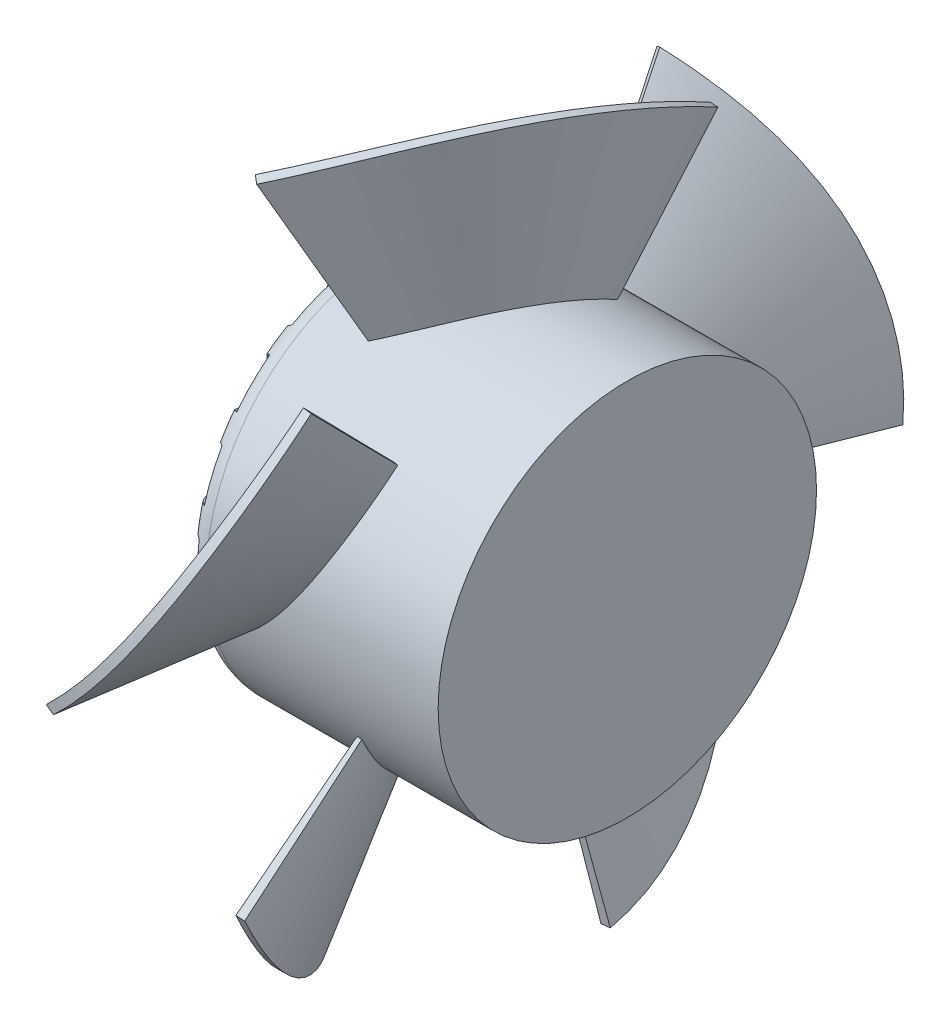
SolidWorks part; units mm, degrees
material "PW100:Mi:0:30:C1:0:1:2:Re:16:"
ref_plane "Front" through (0, 0, 0) normal (0, 0, 1) x (1, 0, 0)
ref_plane "Top" through (0, 0, 0) normal (0, 1, 0) x (1, 0, 0)
ref_plane "Right" through (0, 0, 0) normal (1, 0, 0) x (0, 0, -1)
sketch "Support-Front" plane through (0, 0, 0) normal (0, 0, 1) x (1, 0, 0)
  line L0 (-32, 0) -> (-5, 0) construction
  line L1 (-32, -20) -> (-32, 20)
  line L2 (-32, 20) -> (-5, 20)
  line L3 (-32, -20) -> (-5, -20)
  line L4 (-5, 20) -> (-5, -20)
  line L5 (-18.5, 20) -> (-18.5, -20) construction
  line L6 (-5, 20) -> (0, 20) construction
  line L7 (-5, -20) -> (0, -20) construction
  line L8 (0, 20) -> (0, -20) construction
  line L11 (-18.5, 20) -> (-18.5, 37) construction
  line L12 (-18.5, -20) -> (-18.5, -37) construction
  point P12 (0, 0)
  point P14 (-18.5, 0)
  dimension "Width" = 32
  dimension "Diam-Body" = 40
  dimension "Diam-Fan" = 74
  dimension "Dist-Fan" = 5
sketch "Support-Right" plane through (0, 0, 0) normal (1, 0, 0) x (0, 0, -1)
  line L0 (0, 0) -> (-3.3333, 0) construction
  line L1 (-3.3333, 0) -> (-6.6667, 0) construction
  line L2 (0, 20) -> (-2.4557, 19.1062) construction
  line L3 (-6.6667, 0) -> (-10, 0) construction
  line L4 (-10, 0) -> (-13.3333, 0) construction
  line L6 (0, 20) -> (0, -20) construction
  line L7 (0, 20) -> (0, -20) construction
  line L8 (2.4557, 20) -> (2.4557, 19.1062)
  line L9 (-2.4557, 20) -> (-2.4557, 19.1062)
  line L10 (2.4557, 20) -> (-2.4557, 20)
  line L11 (0, 20) -> (0, 19.1062) construction
  line L12 (0, 19.1062) -> (0, 16.6505) construction
  line L13 (0, 0) -> (-2.4557, 20) construction
  circle A0 centre (0, 0) radius 37
  circle A1 centre (0, 0) radius 13.3333
  circle A2 centre (0, 0) radius 6.6667
  circle A3 centre (0, 0) radius 3.3333
  arc A4 (2.4557, 19.1062) -> (-2.4557, 19.1062) centre (0, 19.1062) cw
  dimension "Diam-Motor" = 26.6667
  dimension "D1" = 7
  dimension "D2" = 20
sketch "Support-Fan-Blade-Top" plane through (0, 0, 0) normal (0, 1, 0) x (-1, 0, 0)
  line L0 (18.5, 0) -> (30.5957, 16.0515) construction
  line L1 (12.6237, -19.2204) -> (30.5957, 16.0515) construction
  line L2 (21.6097, -1.5845) -> (18.5, 0) construction
  line L4 (32, 0) -> (30.5957, 16.0515) construction
  line L5 (32, 0) -> (5, 0) construction
  line L6 (29.9137, 16.7829) -> (30.5957, 16.0515)
  line L7 (11.6312, -19.0986) -> (12.6237, -19.2204)
  arc A0 (30.5957, 16.0515) -> (12.6237, -19.2204) centre (70.0641, -26.2732) ccw
  arc A1 (29.9137, 16.7829) -> (11.6312, -19.0986) centre (70.0641, -26.2732) ccw
  dimension "Angle-Fan-Blade" = 117
  dimension "D1" = 10
  dimension "D3" = 85
  dimension "D2" = 1
ref_plane "Plane-Angle-Fan-Blade" through (-14.687, 0, -7.4834) normal (-0.891, 0, -0.454) x (-0.454, 0, 0.891)
ref_plane "Plane-Top-Fan-Blade" through (0, 37, 0) normal (0, 1, 0) x (-1, 0, 0)
sketch "Sketch-Blade-Bottom" plane through (0, 0, 0) normal (0, 1, 0) x (1, 0, 0)
  point P0 (-18.5, 0)
sketch "Sketch-Blade-Top" plane through (0, 37, 0) normal (0, 1, 0) x (-1, 0, 0)
  line L2 (30.5957, 16.0515) -> (29.9137, 16.7829)
  line L3 (11.6312, -19.0986) -> (12.6237, -19.2204)
  line L4 (30.5957, 16.0515) -> (29.9137, 16.7829)
  line L5 (11.6312, -19.0986) -> (12.6237, -19.2204)
  arc A3 (29.9137, 16.7829) -> (11.6312, -19.0986) centre (70.0641, -26.2732) ccw
  arc A4 (30.5957, 16.0515) -> (12.6237, -19.2204) centre (70.0641, -26.2732) ccw
  arc A5 (29.9137, 16.7829) -> (11.6312, -19.0986) centre (70.0641, -26.2732) ccw
  arc A6 (30.5957, 16.0515) -> (12.6237, -19.2204) centre (70.0641, -26.2732) ccw
  dimension "D1" = 0
ref_plane "Plane-Right-Cut" through (-32, 0, 0) normal (1, 0, 0) x (0, 0, -1)
sketch "Sketch5" plane through (0, 0, 0) normal (0, 0, 1) x (1, 0, 0)
  line L0 (-5, 20) -> (-5, -20) construction
  line L1 (-32, -20) -> (-32, 20) construction
  line L4 (-5, 20) -> (-5, 0)
  line L5 (-32, 0) -> (-32, 20)
  line L6 (-32, 0) -> (-5, 0)
  line L7 (-32, 20) -> (-5, 20) construction
  line L8 (-32, 0) -> (-5, 0) construction
  line L9 (-32, 0) -> (-5, 0) construction
  line L10 (-32, 20) -> (-5, 20)
revolve "Body" add sketch "Sketch5" angle 360 about L9
loft "Loft-Fan-Blade" add profiles "Sketch-Blade-Top", "Sketch-Blade-Bottom"
pattern_circular "CirPattern1" count 5 over 360 about axis through (-32, 0, 0) along (1, 0, 0) of "Loft-Fan-Blade"
sketch "Sketch-Cut-Blade" plane through (0, 0, 0) normal (1, 0, 0) x (0, 0, -1)
  circle A0 centre (0, 0) radius 37 construction
  circle A1 centre (0, 0) radius 37
extrude "Cut-Fan-Blade" cut sketch "Sketch-Cut-Blade" against normal through all flip side to cut
sketch "Sketch6" plane through (-32, 0, 0) normal (1, 0, 0) x (0, 0, -1)
  circle A0 centre (0, 0) radius 13.3333 construction
  circle A1 centre (0, 0) radius 13.3333
extrude "Cut-Body" cut sketch "Sketch6" along normal blind 1.25
sketch "Sketch7" plane through (-32, 0, 0) normal (1, 0, 0) x (0, 0, -1)
  circle A0 centre (0, 0) radius 3.3333 construction
  circle A1 centre (0, 0) radius 6.6667 construction
  circle A2 centre (0, 0) radius 3.3333
  circle A3 centre (0, 0) radius 6.6667
fillet "Cosmetic-Fillet" radius 2.5 1 edges at (-32, 0, 20)
sketch "Sketch8" plane through (-32, 0, 0) normal (1, 0, 0) x (0, 0, -1)
  line L0 (2.4557, 20) -> (2.4557, 19.1062) construction
  line L1 (2.4557, 20) -> (-2.4557, 20) construction
  line L2 (-2.4557, 20) -> (-2.4557, 19.1062) construction
  line L3 (2.4557, 20) -> (2.4557, 19.1062)
  line L4 (2.4557, 20) -> (-2.4557, 20)
  line L5 (-2.4557, 20) -> (-2.4557, 19.1062)
  arc A0 (-2.4557, 19.1062) -> (2.4557, 19.1062) centre (0, 19.1062) ccw construction
  arc A1 (-2.4557, 19.1062) -> (2.4557, 19.1062) centre (0, 19.1062) ccw
extrude "Cut-Body-Cosmetic-Body" cut sketch "Sketch8" along normal up to surface (1.25 mm away) up to face at (-30.75, 0, -13.3333)
pattern_circular "CirPattern-Cut-Body-Cosmetic-Body" count 16 over 360 about axis through (0, 0, 0) along (1, 0, 0) of "Cut-Body-Cosmetic-Body"
extrude "Extrude3" cut sketch "Sketch7" along normal blind 1.6667
equation "\"Angle-Blade@Plane-Angle-Fan-Blade\" = \"Angle-Fan-Blade@Support-Fan-Blade-Top\""
equation "\"Rad@Cosmetic-Fillet\" = \"Dist-Fan@Support-Front\" / 2"
equation "\"Diam-Motor@Support-Right\" = \"Diam-Body@Support-Front\" / 1.5"
equation "\"Depth@Cut-Body\" = \"Dist-Fan@Support-Front\" / 4"
equation "\"D1@Extrude3\" = \"Dist-Fan@Support-Front\" / 3"
